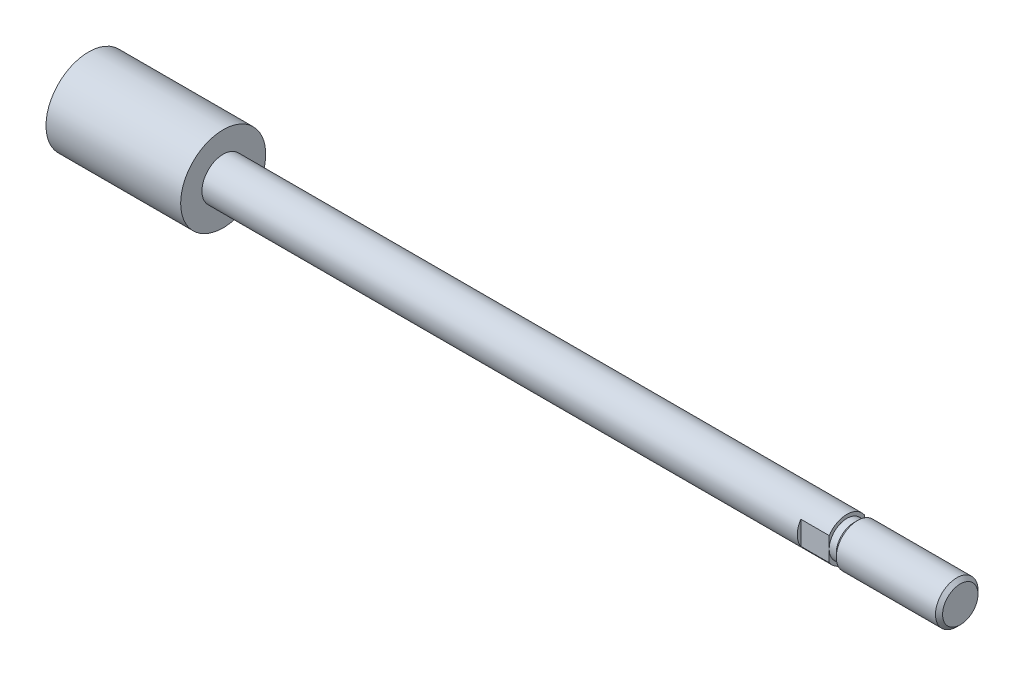
SolidWorks part; units mm, degrees
material "Wrought Stainless Steel"
ref_plane "Front Plane" through (0, 0, 0) normal (0, 0, 1) x (1, 0, 0)
ref_plane "Top Plane" through (0, 0, 0) normal (0, 1, 0) x (1, 0, 0)
ref_plane "Right Plane" through (0, 0, 0) normal (1, 0, 0) x (0, 0, -1)
sketch "Sketch1" plane through (0, 0, 0) normal (0, 0, 1) x (1, 0, 0)
  line L0 (-26.3912, 0) -> (0, 0) construction
  line L1 (0, -6) -> (0, 0)
  line L2 (19, -3) -> (107, -3)
  line L3 (123, -3) -> (123, 0)
  line L4 (0, 0) -> (123, 0)
  line L5 (107, -3) -> (107, -2.5)
  line L6 (107, -2.5) -> (108, -2.5)
  line L7 (108, -2.5) -> (108.5, -3)
  line L8 (108.5, -3) -> (123, -3)
  line L11 (0, -6) -> (19, -6)
  line L14 (19, -3) -> (19, -6)
  dimension "piton L" = 19
  dimension "piston od" = 12
revolve "Revolve1" add sketch "Sketch1" angle 360 about L0
cosmetic thread "Cosmetic Thread1" parameters "D2"=5
chamfer "Chamfer1" distance 0.5 angle 45 1 edges at (123, 0, 3)
sketch "Sketch2" plane through (107, 0, 0) normal (1, 0, 0) x (0, 0, -1)
  line L0 (0, 0) -> (0, 14.809) construction
  line L1 (-6, 6) -> (-2.5, 6)
  line L2 (-6, 6) -> (-6, -6)
  line L3 (-6, -6) -> (-2.5, -6)
  line L4 (-2.5, 6) -> (-2.5, -6)
  line L5 (0, 55) -> (0, -55) construction
  circle A0 centre (0, 0) radius 6 construction
  dimension "D1" = 5
extrude "Cut-Extrude1" cut sketch "Sketch2" against normal blind 4
mirror "Mirror1" about plane through (0, 0, 0) normal (0, 0, 1) of "Cut-Extrude1"
